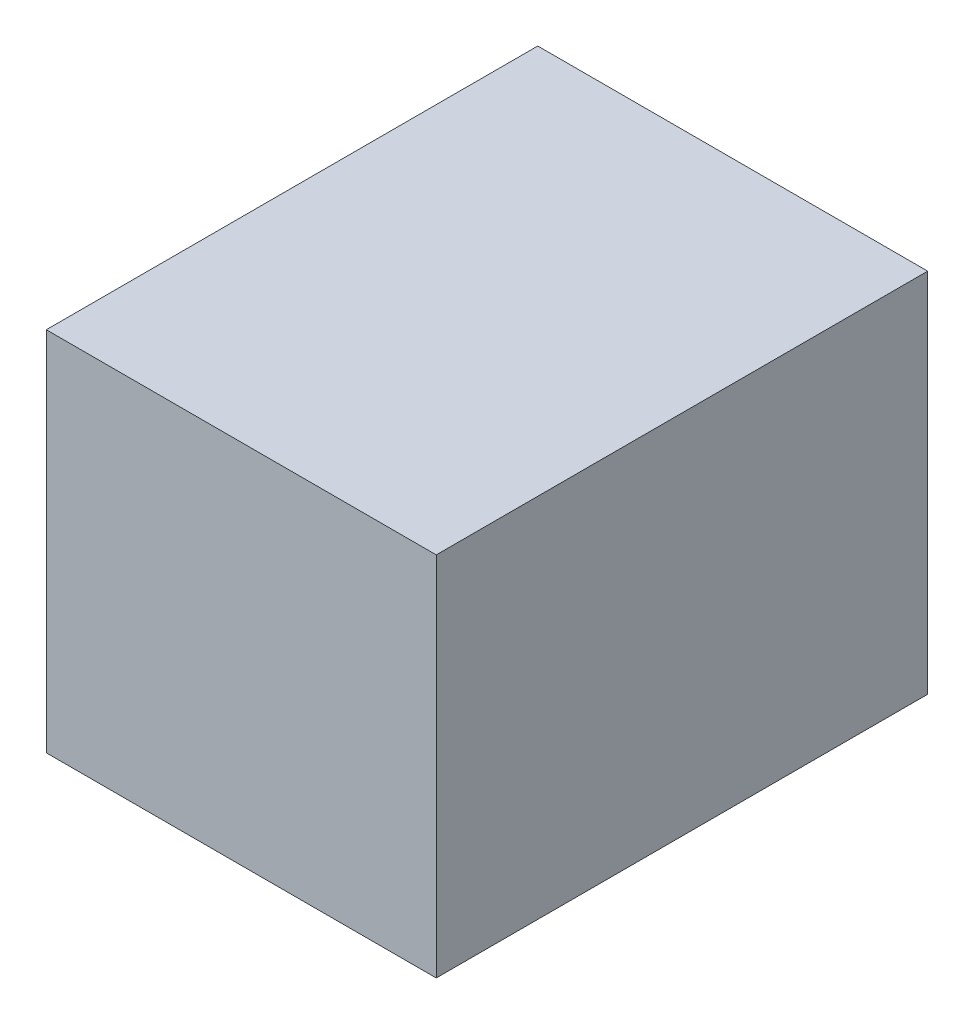
SolidWorks part; units mm, degrees
other "DetailItem1"
ref_plane "Front Plane" through (0, 0, 0) normal (0, 0, 1) x (1, 0, 0)
ref_plane "Top Plane" through (0, 0, 0) normal (0, 1, 0) x (1, 0, 0)
ref_plane "Right Plane" through (0, 0, 0) normal (1, 0, 0) x (0, 0, -1)
sketch "Sketch1" plane through (0, 0, 0) normal (0, 1, 0) x (1, 0, 0)
  line L1 (-18.25, -23) -> (18.25, -23)
  line L2 (-18.25, -23) -> (-18.25, 23)
  line L3 (-18.25, 23) -> (18.25, 23)
  line L4 (18.25, -23) -> (18.25, 23)
  line L5 (-18.25, -23) -> (18.25, 23) construction
  line L6 (-18.25, 23) -> (18.25, -23) construction
  point P0 (0, 0)
  dimension "D1" = 46
  dimension "D2" = 36.5
extrude "Boss-Extrude1" add sketch "Sketch1" along normal blind 34.3
